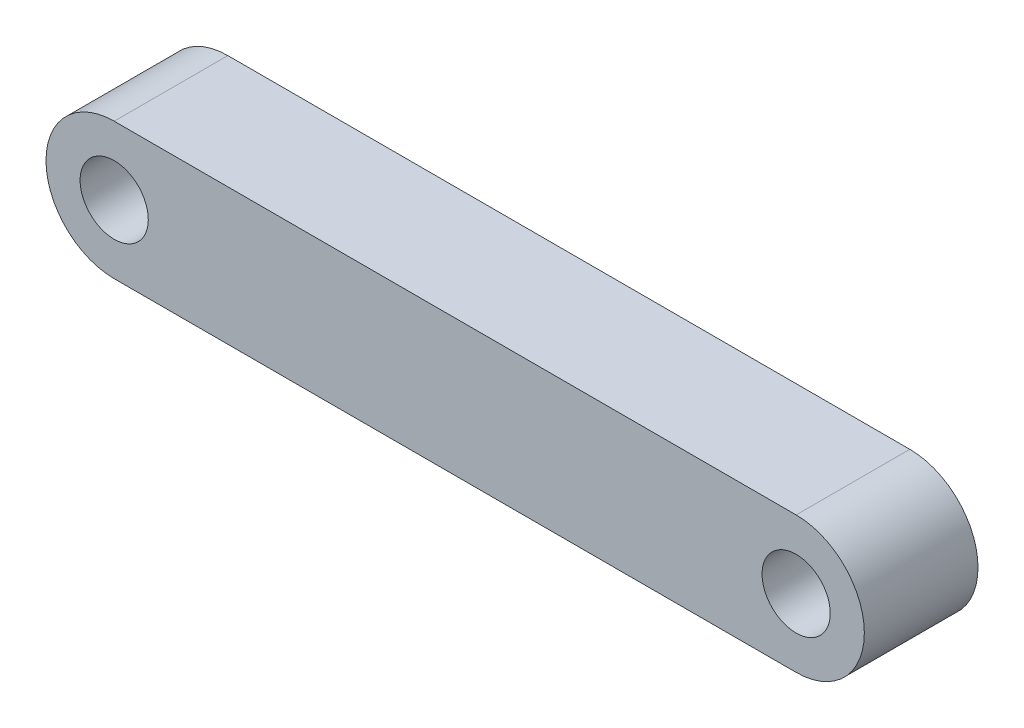
SolidWorks part; units mm, degrees
ref_plane "Front Plane" through (0, 0, 0) normal (0, 0, 1) x (1, 0, 0)
ref_plane "Top Plane" through (0, 0, 0) normal (0, 1, 0) x (1, 0, 0)
ref_plane "Right Plane" through (0, 0, 0) normal (1, 0, 0) x (0, 0, -1)
sketch "Sketch1" plane through (0, 0, 0) normal (0, 0, 1) x (1, 0, 0)
  line L0 (0, 0) -> (30, 0) construction
  line L1 (0, 3) -> (30, 3)
  line L2 (0, -3) -> (30, -3)
  arc A0 (0, 3) -> (0, -3) centre (0, 0) ccw
  arc A1 (30, -3) -> (30, 3) centre (30, 0) ccw
  circle A3 centre (0, 0) radius 1.5
  circle A6 centre (30, 0) radius 1.5
  point P3 (15, 0)
  dimension "D1" = 3
  dimension "D4" = 3
  dimension "D3" = 3
  dimension "D2" = 30
extrude "Boss-Extrude1" add sketch "Sketch1" along normal blind 5
equation "\"D3@Sketch1\"=\"D4@Sketch1\""
